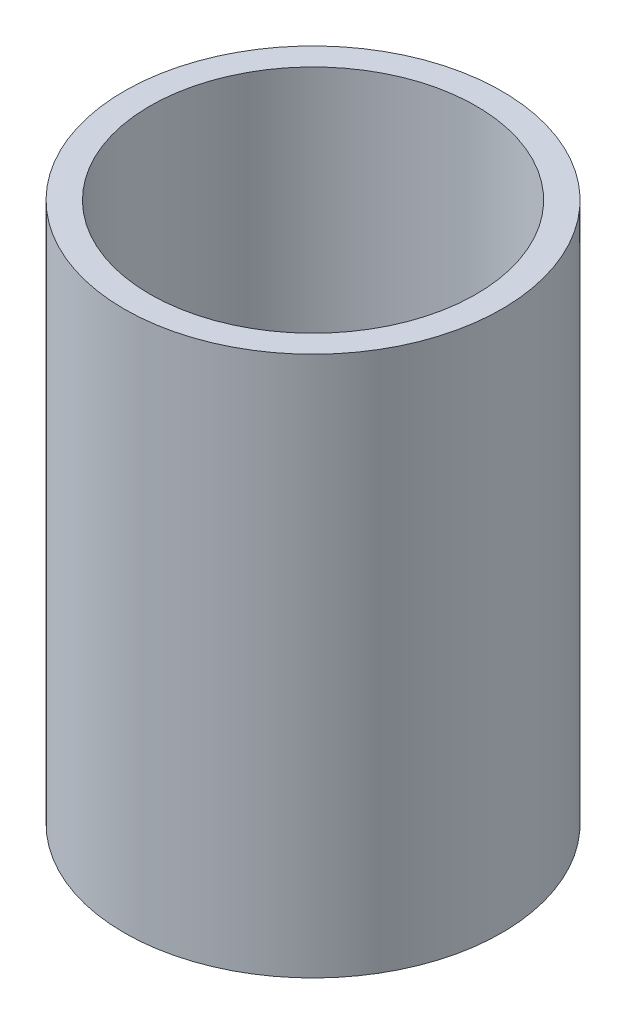
SolidWorks part; units mm, degrees
material "Corrugated Paper"
ref_plane "Front Plane" through (0, 0, 0) normal (0, 0, 1) x (1, 0, 0)
ref_plane "Top Plane" through (0, 0, 0) normal (0, 1, 0) x (1, 0, 0)
ref_plane "Right Plane" through (0, 0, 0) normal (1, 0, 0) x (0, 0, -1)
ref_axis "Axis1" through (0, 55, 0) along (0, -1, 0)
sketch "Sketch1" plane through (0, 0, 0) normal (0, 0, 1) x (1, 0, 0)
  line L1 (-46.609, 45.6176) -> (-40.259, 45.6176)
  line L2 (-46.609, 45.6176) -> (-46.609, -87.7324)
  line L3 (-46.609, -87.7324) -> (-40.259, -87.7324)
  line L4 (-40.259, 45.6176) -> (-40.259, -87.7324)
  line L5 (-38.1, 45.6176) -> (0, 45.6176) construction
  line L6 (-38.1, -87.7324) -> (0, -87.7324) construction
  point P4 (-40.259, 45.6176)
  point P5 (0, 0)
  point P11 (-46.609, 45.6176)
revolve "Revolve1" add sketch "Sketch1" angle 360 about axis through (0, 55, 0) along (0, -1, 0)
